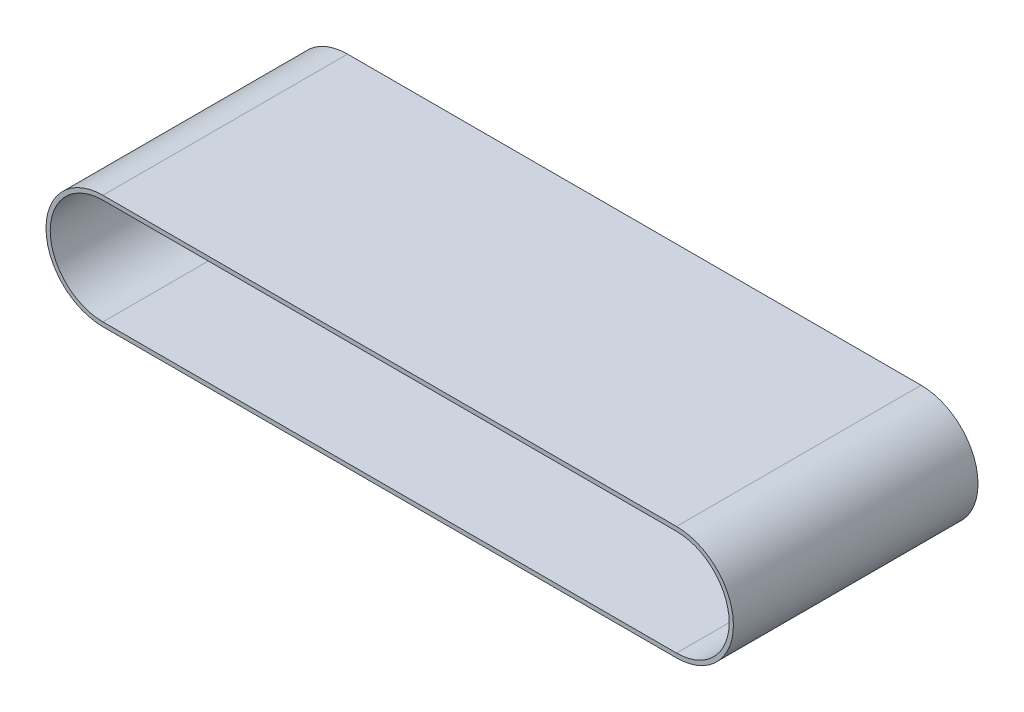
SolidWorks part; units mm, degrees
ref_plane "Front Plane" through (0, 0, 0) normal (0, 0, 1) x (1, 0, 0)
ref_plane "Top Plane" through (0, 0, 0) normal (0, 1, 0) x (1, 0, 0)
ref_plane "Right Plane" through (0, 0, 0) normal (1, 0, 0) x (0, 0, -1)
sketch "Sketch1" plane through (0, 0, 0) normal (0, 0, 1) x (1, 0, 0)
  line L0 (-106.5596, 0) -> (112.0524, 0) construction
  line L1 (0, 49.3662) -> (0, -51.426) construction
  line L2 (-83.1586, 11.1371) -> (52.8414, 11.1371)
  line L3 (-83.1586, -13.8629) -> (52.8414, -13.8629)
  line L4 (-83.1586, 11.1371) -> (-83.1586, -13.8629) construction
  line L5 (52.8414, 11.1371) -> (52.8414, -13.8629) construction
  line L6 (-83.1586, 12.1371) -> (52.8414, 12.1371)
  line L7 (52.8414, -14.8629) -> (-83.1586, -14.8629)
  arc A0 (-83.1586, -13.8629) -> (-83.1586, 11.1371) centre (-83.1586, -1.3629) cw
  arc A1 (52.8414, -13.8629) -> (52.8414, 11.1371) centre (52.8414, -1.3629) ccw
  arc A2 (-83.1586, 12.1371) -> (-83.1586, -14.8629) centre (-83.1586, -1.3629) ccw
  arc A3 (52.8414, 12.1371) -> (52.8414, -14.8629) centre (52.8414, -1.3629) cw
  dimension "D1" = 25
  dimension "D2" = 25
  dimension "D3" = 1
  dimension "D4" = 1
  dimension "D5" = 136
  dimension "D6" = 136
extrude "Boss-Extrude1" add sketch "Sketch1" along normal blind 58 contours A3 L6 A2 L7 A1 L3 A0 L2
